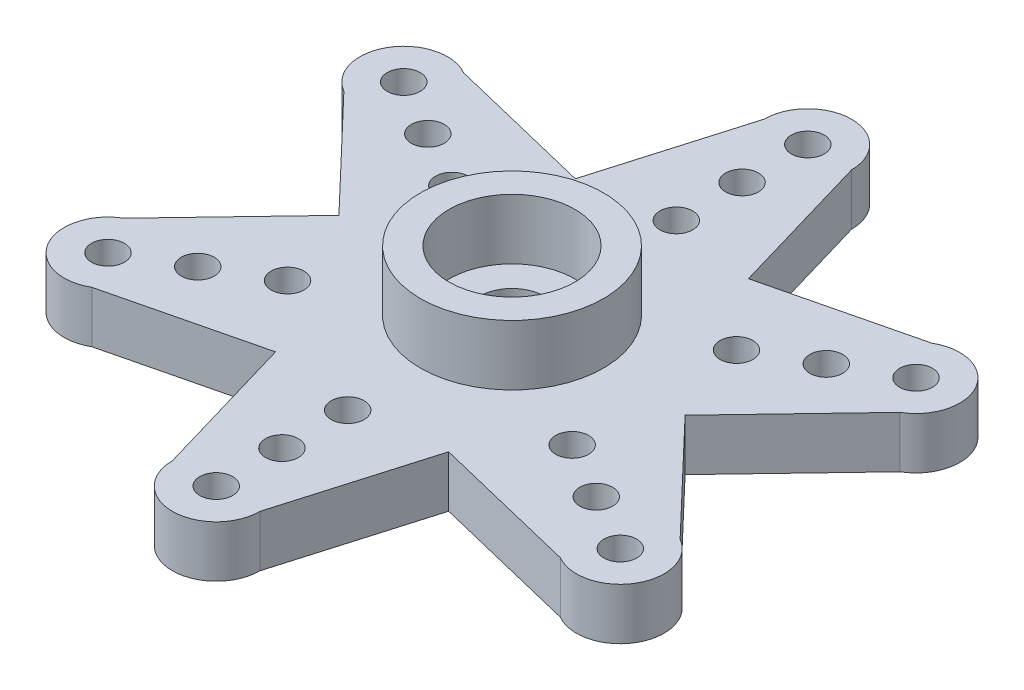
SolidWorks part; units mm, degrees
ref_plane "Front Plane" through (0, 0, 0) normal (0, 0, 1) x (1, 0, 0)
ref_plane "Top Plane" through (0, 0, 0) normal (0, 1, 0) x (1, 0, 0)
ref_plane "Right Plane" through (0, 0, 0) normal (1, 0, 0) x (0, 0, -1)
sketch "Sketch1" plane through (0, 0, 0) normal (0, 1, 0) x (1, 0, 0)
  line L0 (3.95, 6.8416) -> (10.6913, 8.4821)
  line L4 (-3.95, 6.8416) -> (-2, 13.5)
  line L5 (3.95, 6.8416) -> (2, 13.5)
  line L6 (7.9, 0) -> (12.6913, 5.0179)
  line L7 (7.9, 0) -> (12.6913, -5.0179)
  line L8 (3.95, -6.8416) -> (10.6913, -8.4821)
  line L9 (3.95, -6.8416) -> (2, -13.5)
  line L10 (-3.95, -6.8416) -> (-2, -13.5)
  line L11 (-3.95, -6.8416) -> (-10.6913, -8.4821)
  line L12 (-7.9, 0) -> (-12.6913, -5.0179)
  line L13 (-7.9, 0) -> (-12.6913, 5.0179)
  line L14 (-3.95, 6.8416) -> (-10.6913, 8.4821)
  line L15 (3.95, 6.8416) -> (10.6913, 8.4821)
  line L16 (7.9, 0) -> (12.6913, 5.0179)
  line L19 (7.9, 0) -> (12.6913, -5.0179)
  line L20 (3.95, -6.8416) -> (10.6913, -8.4821)
  line L23 (3.95, -6.8416) -> (2, -13.5)
  line L24 (-3.95, -6.8416) -> (-2, -13.5)
  line L27 (-3.95, -6.8416) -> (-10.6913, -8.4821)
  line L28 (-7.9, 0) -> (-12.6913, -5.0179)
  line L31 (-7.9, 0) -> (-12.6913, 5.0179)
  line L32 (-3.95, 6.8416) -> (-10.6913, 8.4821)
  circle A0 centre (0, 0) radius 15.5
  circle A1 centre (0, 10.5) radius 0.75
  arc A2 (10.6913, 8.4821) -> (12.6913, 5.0179) centre (11.6913, 6.75) cw
  arc A3 (-2, 13.5) -> (2, 13.5) centre (0, 13.5) cw
  arc A4 (12.6913, -5.0179) -> (10.6913, -8.4821) centre (11.6913, -6.75) cw
  arc A5 (2, -13.5) -> (-2, -13.5) centre (0, -13.5) cw
  arc A6 (-10.6913, -8.4821) -> (-12.6913, -5.0179) centre (-11.6913, -6.75) cw
  arc A7 (-12.6913, 5.0179) -> (-10.6913, 8.4821) centre (-11.6913, 6.75) cw
  arc A8 (10.6913, 8.4821) -> (12.6913, 5.0179) centre (11.6913, 6.75) cw
  arc A9 (12.6913, -5.0179) -> (10.6913, -8.4821) centre (11.6913, -6.75) cw
  arc A10 (2, -13.5) -> (-2, -13.5) centre (0, -13.5) cw
  arc A11 (-10.6913, -8.4821) -> (-12.6913, -5.0179) centre (-11.6913, -6.75) cw
  arc A12 (-12.6913, 5.0179) -> (-10.6913, 8.4821) centre (-11.6913, 6.75) cw
  circle A13 centre (0, 13.5) radius 0.75
  circle A14 centre (0, 7.5) radius 0.75
  circle A15 centre (11.6913, 6.75) radius 0.75
  circle A16 centre (9.0933, 5.25) radius 0.75
  circle A17 centre (6.4952, 3.75) radius 0.75
  circle A18 centre (11.6913, -6.75) radius 0.75
  circle A19 centre (9.0933, -5.25) radius 0.75
  circle A20 centre (6.4952, -3.75) radius 0.75
  circle A21 centre (0, -13.5) radius 0.75
  circle A22 centre (0, -10.5) radius 0.75
  circle A23 centre (0, -7.5) radius 0.75
  circle A24 centre (-11.6913, -6.75) radius 0.75
  circle A25 centre (-9.0933, -5.25) radius 0.75
  circle A26 centre (-6.4952, -3.75) radius 0.75
  circle A27 centre (-11.6913, 6.75) radius 0.75
  circle A28 centre (-9.0933, 5.25) radius 0.75
  circle A29 centre (-6.4952, 3.75) radius 0.75
  point P94 (0, 0)
  dimension "D1" = 6
  dimension "D2" = 6
extrude "Boss-Extrude1" add sketch "Sketch1" along normal blind 2.35 contours A7 L13 L12 A6 L11 L10 A5 L9 L8 A4 L7 L6 A2 L0 L5 A3 L4 L14 A29 A28 A27 A26 A25 A24 A23 A22 A21 A20 A19 A18 A17
sketch "Sketch2" plane through (0, 2.35, 0) normal (0, 1, 0) x (1, 0, 0)
  line L0 (-3.95, 6.8416) -> (3.95, -6.8416) construction
  line L1 (-7.9, 0) -> (7.9, 0) construction
  circle A0 centre (0, 0) radius 1.5
  circle A1 centre (0, 0) radius 2.5485
  circle A2 centre (0, 0) radius 4.18
extrude "Cut-Extrude1" cut sketch "Sketch2" against normal blind 2.35 contours A0
sketch "Sketch3" plane through (0, 2.35, 0) normal (0, 1, 0) x (1, 0, 0)
  circle A0 centre (0, 0) radius 2.875
  circle A1 centre (0, 0) radius 4.18
extrude "Boss-Extrude2" add sketch "Sketch3" along normal blind 2.75
